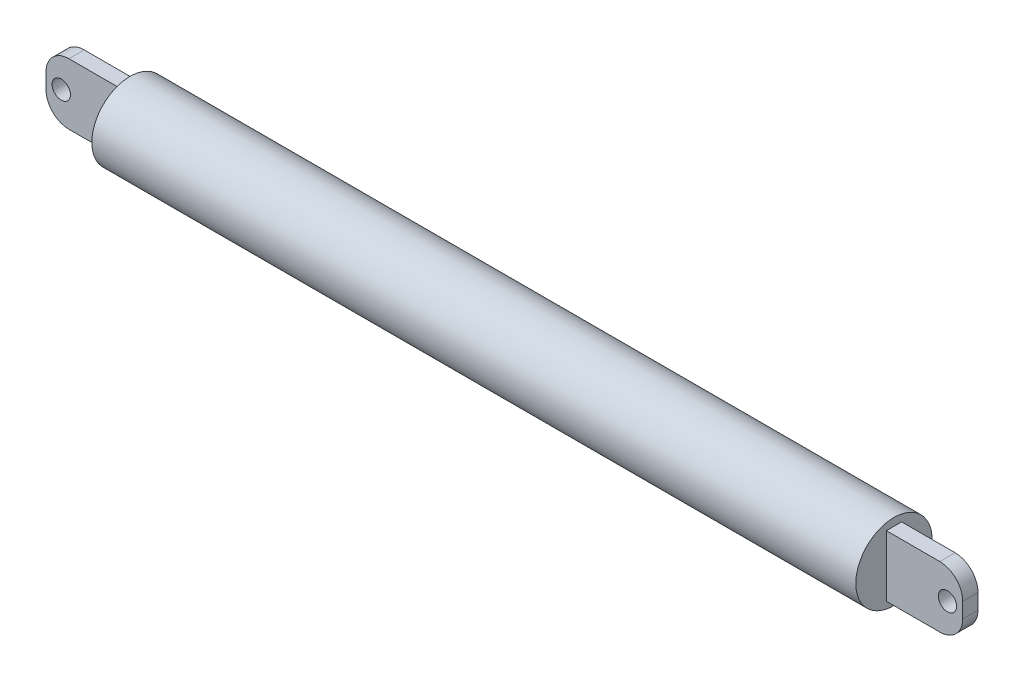
SolidWorks part; units mm, degrees
ref_plane "Plano frontal" through (0, 0, 0) normal (0, 0, 1) x (1, 0, 0)
ref_plane "Plano superior" through (0, 0, 0) normal (0, 1, 0) x (1, 0, 0)
ref_plane "Plano direito" through (0, 0, 0) normal (1, 0, 0) x (0, 0, -1)
sketch "Esboço1" plane through (0, 0, 0) normal (0, 0, 1) x (1, 0, 0)
  line L0 (0, 0) -> (0, 193.2127) construction
  line L1 (0, 0) -> (319.2409, 0) construction
  line L2 (-250, 25) -> (250, 25)
  line L3 (250, 25) -> (250, 0)
  line L4 (250, 0) -> (-250, 0)
  line L5 (-250, 25) -> (-250, 0)
  point P9 (0, 25)
  dimension "D1" = 500
  dimension "D2" = 50
revolve "Revolução1" add sketch "Esboço1" angle 360 about L1
sketch "Esboço2" plane through (0, 0, 0) normal (0, 0, 1) x (1, 0, 0)
  line L0 (250, -20) -> (250, 20)
  line L1 (250, -25) -> (250, 25) construction
  line L2 (250, 20) -> (285, 20)
  line L3 (300, 5) -> (300, -5)
  line L4 (250, 0) -> (300, 0) construction
  line L5 (250, -20) -> (285, -20)
  circle A0 centre (290, 0) radius 6
  arc A1 (285, 20) -> (300, 5) centre (285, 5) cw
  arc A2 (285, -20) -> (300, -5) centre (285, -5) ccw
  point P10 (300, 20)
  dimension "D1" = 12
  dimension "D5" = 15
  dimension "D2" = 40
  dimension "D3" = 50
  dimension "D4" = 40
extrude "Ressalto-extrusão1" add sketch "Esboço2" along normal mid plane 10
mirror "Espelhar1" about plane through (0, 0, 0) normal (1, 0, 0) of "Ressalto-extrusão1"
